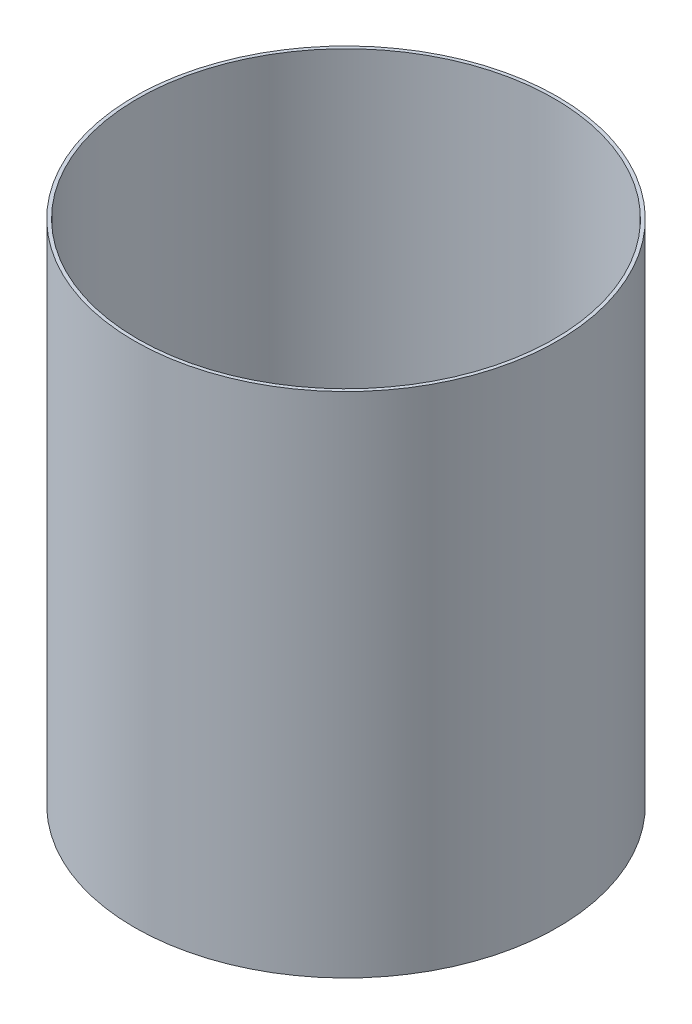
SolidWorks part; units mm, degrees
ref_plane "Front Plane" through (0, 0, 0) normal (0, 0, 1) x (1, 0, 0)
ref_plane "Top Plane" through (0, 0, 0) normal (0, 1, 0) x (1, 0, 0)
ref_plane "Right Plane" through (0, 0, 0) normal (1, 0, 0) x (0, 0, -1)
sketch "Sketch1" plane through (0, 0, 0) normal (0, 1, 0) x (1, 0, 0)
  circle A0 centre (0, 0) radius 125
  circle A1 centre (0, 0) radius 123
  dimension "D1" = 250
  dimension "D2" = 2
extrude "Boss-Extrude1" add sketch "Sketch1" along normal blind 300
